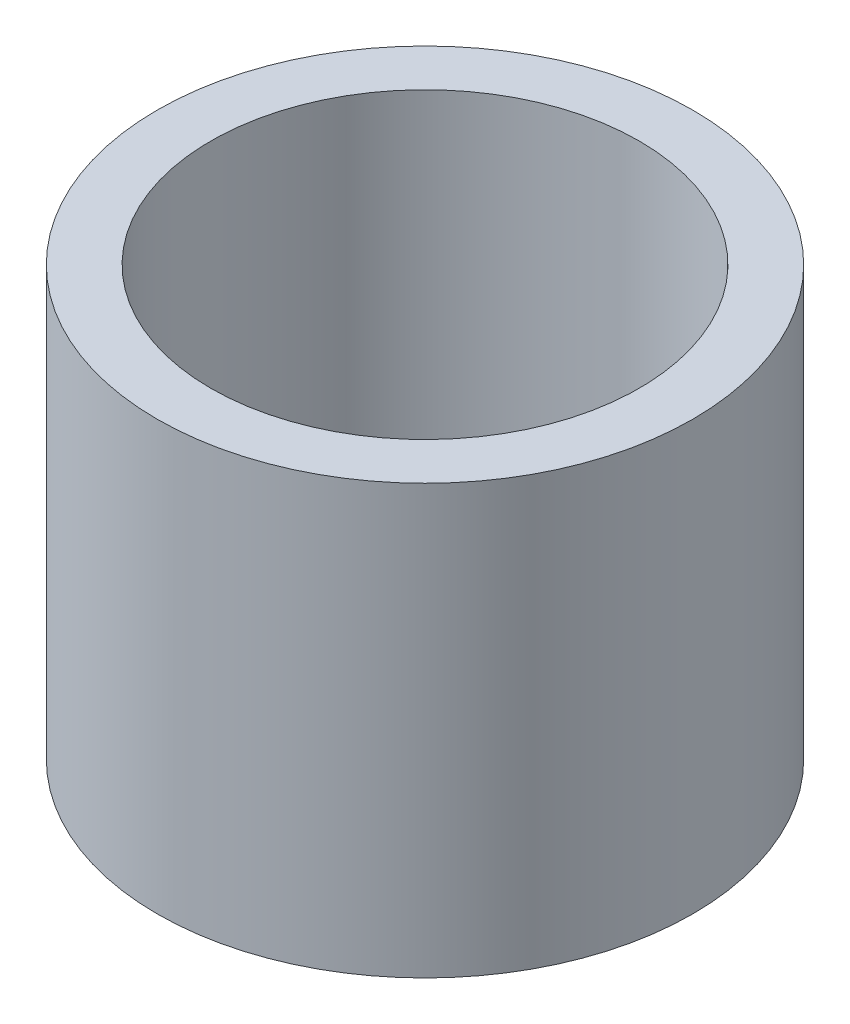
SolidWorks part; units mm, degrees
ref_plane "Front Plane" through (0, 0, 0) normal (0, 0, 1) x (1, 0, 0)
ref_plane "Top Plane" through (0, 0, 0) normal (0, 1, 0) x (1, 0, 0)
ref_plane "Right Plane" through (0, 0, 0) normal (1, 0, 0) x (0, 0, -1)
sketch "Sketch1" plane through (0, 0, 0) normal (0, 1, 0) x (1, 0, 0)
  circle A0 centre (0, 0) radius 15.875
  circle A1 centre (0, 0) radius 12.7
  dimension "D1" = 25.4
  dimension "D2" = 31.75
extrude "Boss-Extrude1" add sketch "Sketch1" along normal blind 25.4
